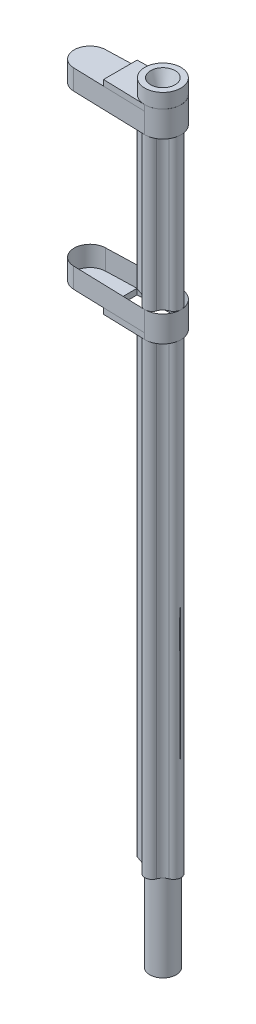
SolidWorks part; units mm, degrees
ref_plane "Alzado" through (0, 0, 0) normal (0, 0, 1) x (1, 0, 0)
ref_plane "Planta" through (0, 0, 0) normal (0, 1, 0) x (1, 0, 0)
ref_plane "Vista lateral" through (0, 0, 0) normal (1, 0, 0) x (0, 0, -1)
sketch "Croquis1" plane through (0, 0, 0) normal (0, 1, 0) x (1, 0, 0)
  line L0 (-9.8937, 10.1905) -> (-9.8937, -2.3095) construction
  line L1 (-18.0798, 3.9556) -> (-3.5798, 3.9556) construction
  line L2 (-14.4799, 6.3444) -> (-17.2852, 5.3731)
  line L3 (-14.4799, 1.5669) -> (-17.2852, 2.5382)
  arc A0 (-12.2884, -0.6136) -> (-14.4799, 1.5669) centre (-15.6437, -1.7944) ccw
  arc A1 (-7.499, -0.6136) -> (-5.3355, 1.557) centre (-4.1437, -1.7944) cw
  arc A2 (-7.4907, 8.5013) -> (-5.3355, 6.3542) centre (-4.1437, 9.7056) ccw
  arc A3 (-12.2968, 8.5013) -> (-14.4799, 6.3444) centre (-15.6437, 9.7056) cw
  arc A4 (-12.2884, -0.6136) -> (-7.499, -0.6136) centre (-9.8937, 0.2291) ccw
  arc A5 (-5.3355, 1.557) -> (-5.3355, 6.3542) centre (-6.1885, 3.9556) ccw
  arc A7 (-7.4907, 8.5013) -> (-12.2968, 8.5013) centre (-9.8937, 7.6366) ccw
  arc A8 (-17.2852, 5.3731) -> (-17.2852, 2.5382) centre (-16.7944, 3.9556) ccw
  dimension "D1" = 14.5
  dimension "D2" = 3
  dimension "D3" = 5.75
  dimension "D4" = 5.75
  dimension "D5" = 12.5
extrude "Saliente-Extruir2" add sketch "Croquis1" along normal blind 223
sketch "Croquis5" plane through (0, 223, 0) normal (0, 1, 0) x (1, 0, 0)
  line L0 (-3.6695, 3.9405) -> (-40.6695, 3.9405) construction
  line L1 (-10.0793, 10.1886) -> (-35.3329, 9.4381)
  line L2 (-10.0793, -2.3077) -> (-35.3329, -1.5571)
  arc A0 (-10.0793, -2.3077) -> (-10.0793, 10.1886) centre (-9.8936, 3.9405) ccw
  arc A1 (-35.3329, 9.4381) -> (-35.3329, -1.5571) centre (-35.1695, 3.9405) ccw
  arc A4 (-5.3355, 1.557) -> (-5.3355, 6.3542) centre (-6.1885, 3.9556) ccw construction
  dimension "D1" = 37
  dimension "D2" = 11
extrude "Saliente-Extruir3" add sketch "Croquis5" along normal blind 7
sketch "Croquis6" plane through (0, 230, 0) normal (0, 1, 0) x (1, 0, 0)
  line L0 (-24.6695, 9.755) -> (-10.1052, 10.1878)
  line L1 (-10.0793, 10.1886) -> (-35.3329, 9.4381) construction
  line L2 (-24.6695, 9.755) -> (-24.6695, -1.874)
  line L3 (-24.6695, -1.874) -> (-10.1052, -2.3068)
  arc A2 (-10.1052, -2.3068) -> (-10.1052, 10.1878) centre (-9.8936, 3.9405) ccw
extrude "Saliente-Extruir4" add sketch "Croquis6" along normal blind 2
sketch "Croquis7" plane through (0, 232, 0) normal (0, 1, 0) x (1, 0, 0)
  circle A0 centre (-9.9196, 3.9405) radius 6.2501
extrude "Saliente-Extruir5" add sketch "Croquis7" along normal blind 5
sketch "Croquis8" plane through (0, 237, 0) normal (0, 1, 0) x (1, 0, 0)
  circle A0 centre (-9.9196, 3.9405) radius 4.25
  dimension "D1" = 8.5
ref_plane "Plano2" through (0, 229, 0) normal (0, 1, 0) x (1, 0, 0)
sketch "Croquis9" plane through (0, 229, 0) normal (0, 1, 0) x (1, 0, 0)
  circle A0 centre (-9.9196, 3.9405) radius 1
  dimension "D1" = 2
loft "Cortar-Recubrir1" cut profiles "Croquis8", "Croquis9"
ref_plane "Plano3" through (0, 196.75, 0) normal (0, -1, 0) x (-1, 0, 0)
mirror "Simetría3" about plane through (0, 196.75, 0) normal (0, -1, 0) of "Saliente-Extruir3"
mirror "Simetría4" about plane through (0, 196.75, 0) normal (0, -1, 0) of "Saliente-Extruir4"
sketch "Croquis10" plane through (0, 0, 0) normal (0, -1, 0) x (1, 0, 0)
  circle A0 centre (-9.8937, -3.9556) radius 4.5747
  arc A5 (-12.2968, -8.5013) -> (-14.4799, -6.3444) centre (-15.6437, -9.7056) ccw construction
  arc A6 (-7.499, 0.6136) -> (-5.3355, -1.557) centre (-4.1437, 1.7944) ccw construction
extrude "Saliente-Extruir6" add sketch "Croquis10" along normal blind 30
ref_plane "Plano4" through (0, 103.5, 0) normal (0, -1, 0) x (-1, 0, 0)
mirror "Simetría5" about plane through (0, 103.5, 0) normal (0, -1, 0) of "Cortar-Recubrir1"
